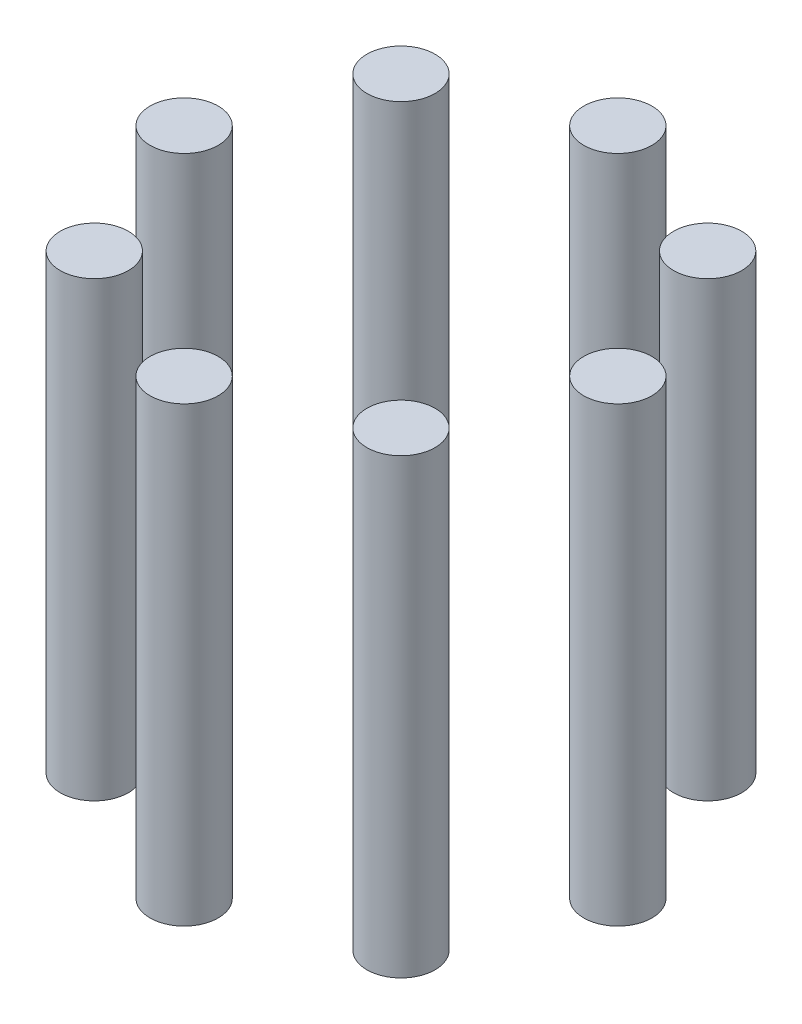
SolidWorks part; units mm, degrees
ref_plane "Front Plane" through (0, 0, 0) normal (0, 0, 1) x (1, 0, 0)
ref_plane "Top Plane" through (0, 0, 0) normal (0, 1, 0) x (1, 0, 0)
ref_plane "Right Plane" through (0, 0, 0) normal (1, 0, 0) x (0, 0, -1)
sketch "Sketch1" plane through (0, 0, 0) normal (0, 1, 0) x (1, 0, 0)
  circle A0 centre (0, 0) radius 35
  circle A1 centre (-35, 0) radius 5.5
  circle A2 centre (-24.7487, 24.7487) radius 5.5
  circle A3 centre (0, 35) radius 5.5
  circle A4 centre (24.7487, 24.7487) radius 5.5
  circle A5 centre (35, 0) radius 5.5
  circle A6 centre (24.7487, -24.7487) radius 5.5
  circle A7 centre (0, -35) radius 5.5
  circle A8 centre (-24.7487, -24.7487) radius 5.5
  point P21 (0, 0)
extrude "Boss-Extrude1" add sketch "Sketch1" along normal blind 73 contours A1 | A2 | A3 | A4 | A5 | A6 | A7 | A8
